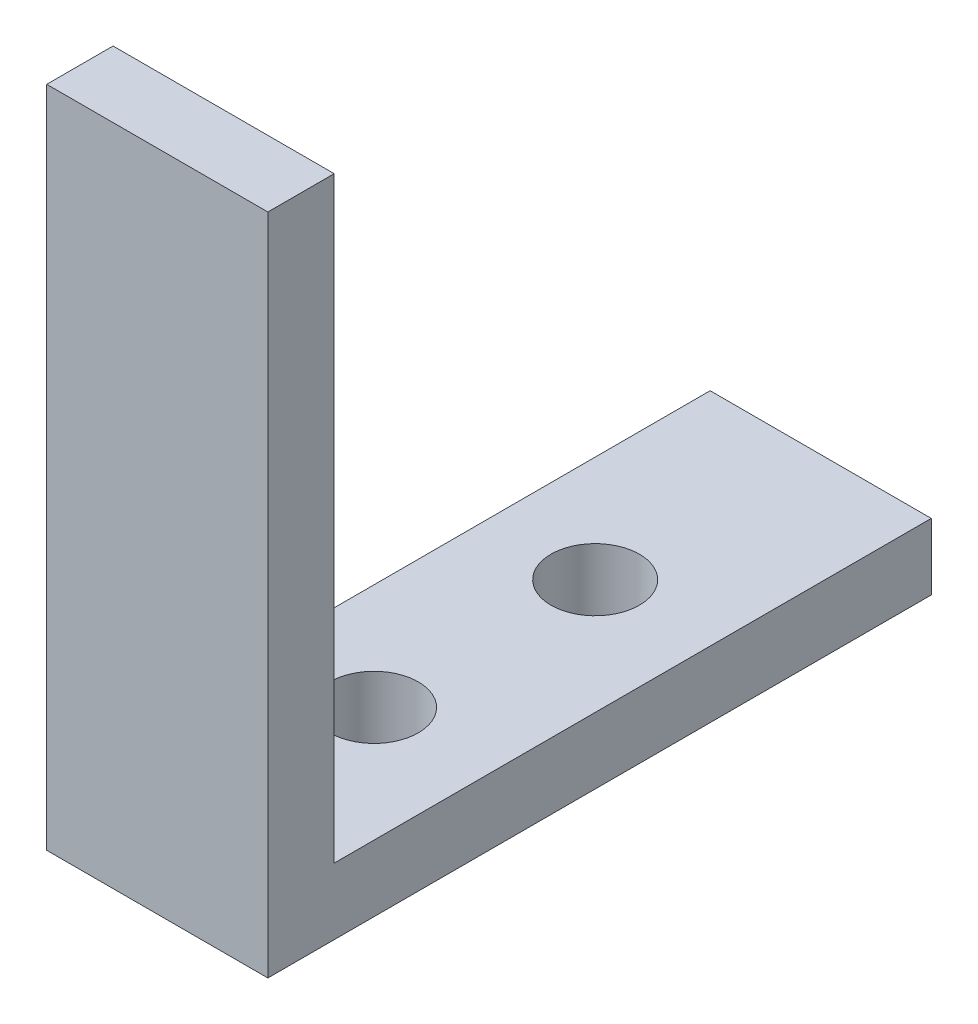
SolidWorks part; units mm, degrees
material "Aluminum Bronze"
ref_plane "Front Plane" through (0, 0, 0) normal (0, 0, 1) x (1, 0, 0)
ref_plane "Top Plane" through (0, 0, 0) normal (0, 1, 0) x (1, 0, 0)
ref_plane "Right Plane" through (0, 0, 0) normal (1, 0, 0) x (0, 0, -1)
sketch "Sketch1" plane through (0, 0, 0) normal (1, 0, 0) x (0, 0, -1)
  line L0 (0, 30) -> (0, 0)
  line L1 (0, 0) -> (30, 0)
  line L2 (30, 0) -> (30, 3)
  line L3 (30, 3) -> (3, 3)
  line L4 (3, 3) -> (3, 30)
  line L5 (3, 30) -> (0, 30)
  dimension "D1" = 3
  dimension "D2" = 3
  dimension "D3" = 30
  dimension "D4" = 30
extrude "Boss-Extrude1" add sketch "Sketch1" along normal blind 10
sketch "Sketch2" plane through (0, 3, 0) normal (0, 1, 0) x (1, 0, 0)
  line L0 (10, 3) -> (0, 3) construction
  circle A0 centre (4.802, 10) radius 2
  circle A1 centre (4.802, 20) radius 2
  point P7 (5, 3)
  dimension "D1" = 7
  dimension "D2" = 10
extrude "Cut-Extrude1" cut sketch "Sketch2" against normal blind 3
